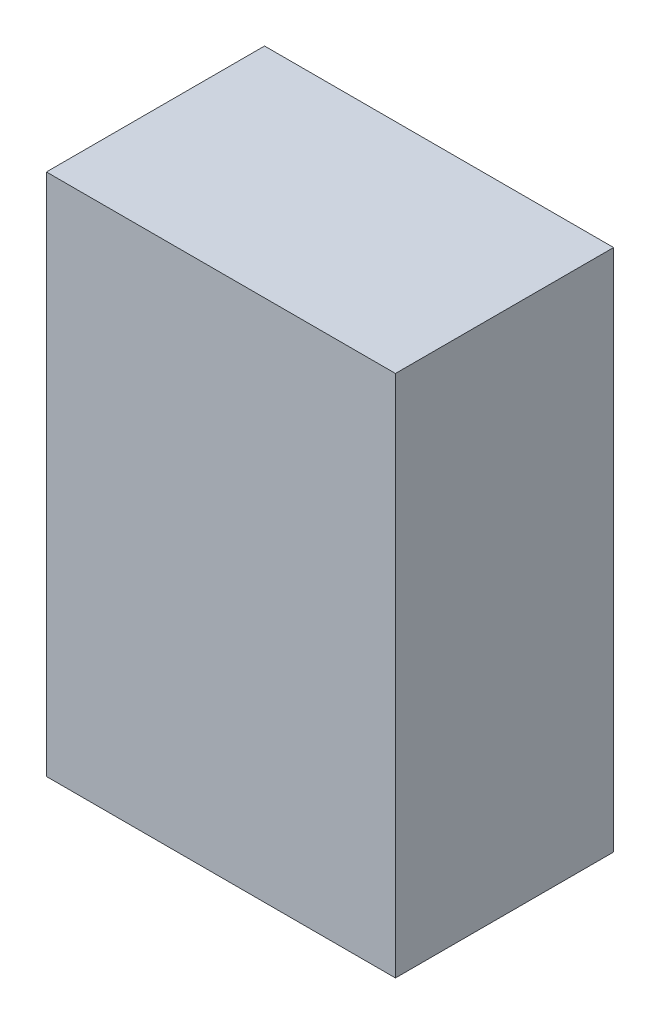
SolidWorks part; units mm, degrees
ref_plane "Front Plane" through (0, 0, 0) normal (0, 0, 1) x (1, 0, 0)
ref_plane "Top Plane" through (0, 0, 0) normal (0, 1, 0) x (1, 0, 0)
ref_plane "Right Plane" through (0, 0, 0) normal (1, 0, 0) x (0, 0, -1)
sketch "Sketch1" plane through (0, 0, 0) normal (0, 1, 0) x (1, 0, 0)
  line L1 (-4000, -2500) -> (4000, -2500)
  line L2 (-4000, -2500) -> (-4000, 2500)
  line L3 (-4000, 2500) -> (4000, 2500)
  line L4 (4000, -2500) -> (4000, 2500)
  line L5 (-4000, -2500) -> (4000, 2500) construction
  line L6 (-4000, 2500) -> (4000, -2500) construction
  point P0 (0, 0)
  dimension "D1" = 8000
  dimension "D2" = 5000
extrude "Boss-Extrude1" add sketch "Sketch1" along normal blind 4000 and the other way blind 8000
